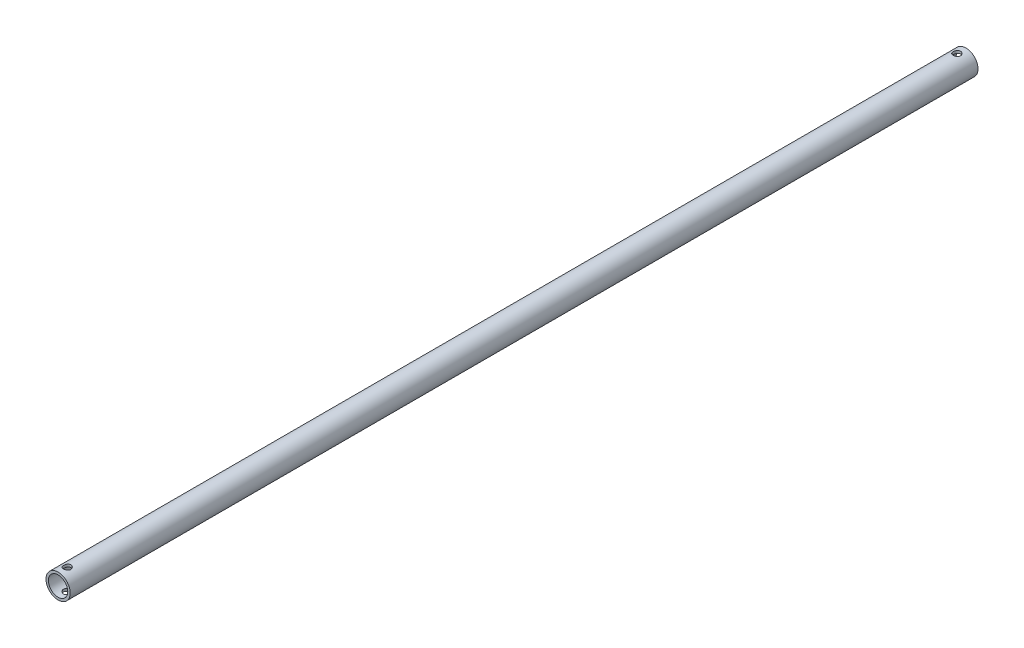
SolidWorks part; units mm, degrees
ref_plane "Płaszczyzna przednia" through (0, 0, 0) normal (0, 0, 1) x (1, 0, 0)
ref_plane "Płaszczyzna górna" through (0, 0, 0) normal (0, 1, 0) x (1, 0, 0)
ref_plane "Płaszczyzna prawa" through (0, 0, 0) normal (1, 0, 0) x (0, 0, -1)
sketch "Szkic1" plane through (0, 0, 0) normal (0, 0, 1) x (1, 0, 0)
  circle A0 centre (0, 0) radius 10
  dimension "D1" = 20
extrude "Dodanie-wyciągnięcie2" add sketch "Szkic1" along normal blind 750
sketch "Szkic3" plane through (0, 0, 750) normal (0, 0, 1) x (1, 0, 0)
  circle A0 centre (0, 0) radius 8
  dimension "D1" = 16
extrude "Wytnij-wyciągnięcie1" cut sketch "Szkic3" against normal through all
sketch "Szkic4" plane through (0, 0, 0) normal (0, 1, 0) x (1, 0, 0)
  circle A0 centre (0, -7.5) radius 3
  dimension "D1" = 6
  dimension "D2" = 7.5
extrude "Wytnij-wyciągnięcie2" cut sketch "Szkic4" against normal through all both and the other way through all
ref_plane "Plane1" through (0, 0, 375) normal (0, 0, 1) x (1, 0, 0)
mirror "Mirror1" about plane through (0, 0, 375) normal (0, 0, 1) of "Wytnij-wyciągnięcie2"
